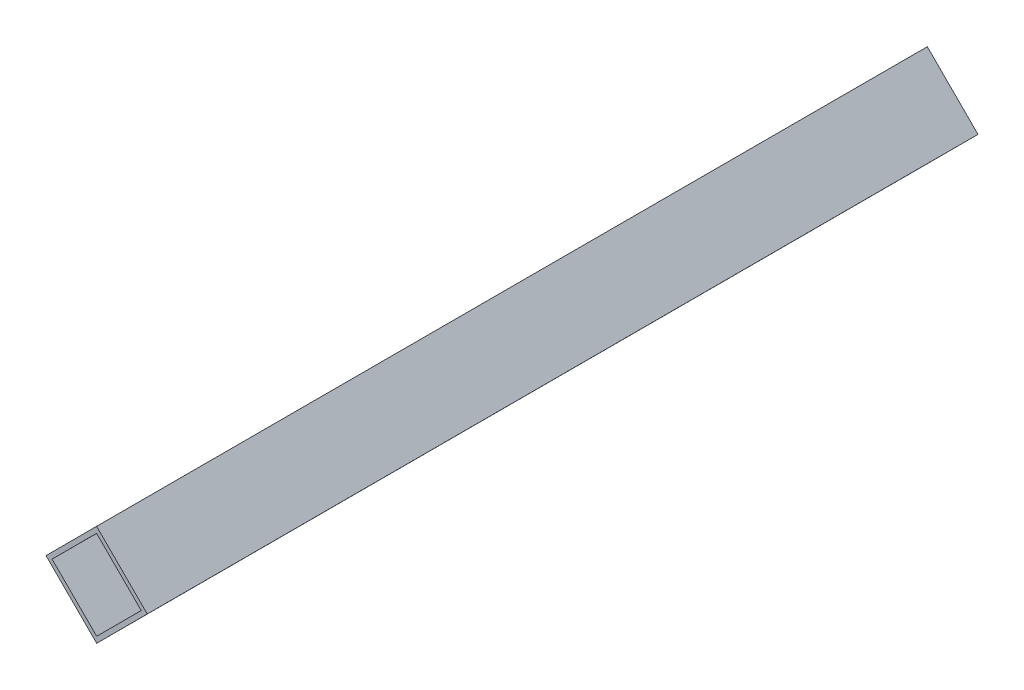
SolidWorks part; units mm, degrees
material "可鍛鑄鐵"
ref_plane "前基準面" through (0, 0, 0) normal (0, 0, 1) x (1, 0, 0)
ref_plane "上基準面" through (0, 0, 0) normal (0, 1, 0) x (1, 0, 0)
ref_plane "右基準面" through (0, 0, 0) normal (1, 0, 0) x (0, 0, -1)
sketch "草圖1" plane through (0, 0, 0) normal (0, 0, 1) x (1, 0, 0)
  line L0 (0, 0) -> (17.6938, -17.6615)
  line L1 (0, 0) -> (-17.6615, -17.6938)
  line L2 (17.6938, -17.6615) -> (0.0323, -35.3553)
  line L3 (-17.6615, -17.6938) -> (0.0323, -35.3553)
  line L4 (0.0019, -2.1213) -> (-15.5402, -17.6919)
  line L5 (0.0019, -2.1213) -> (15.5725, -17.6635)
  line L6 (-15.5402, -17.6919) -> (0.0303, -33.234)
  line L7 (15.5725, -17.6635) -> (0.0303, -33.234)
  point P0 (8.8469, -8.8308)
  dimension "D1" = 25
  dimension "D2" = 25
  dimension "D3" = 1.5
  dimension "D4" = 1.5
  dimension "D5" = 1.5
  dimension "D6" = 1.5
extrude "填料-伸長1" add sketch "草圖1" along normal blind 290
sketch "草圖2" plane through (0, 0, 0) normal (0.7065, 0.7078, 0) x (0.7078, -0.7065, 0)
  line L0 (25, -290) -> (0, -290) construction
  line L1 (25, -290) -> (25, 0) construction
  line L2 (25, 0) -> (0, 0) construction
  line L3 (0, -290) -> (0, 0) construction
  circle A0 centre (12.5, -143) radius 2.75
  circle A1 centre (12.5, -187) radius 2.75
  circle A2 centre (12.5, -103) radius 2.75
  circle A3 centre (12.5, -147) radius 2.75
  dimension "D1" = 5.5
  dimension "D2" = 5.5
  dimension "D4" = 103
  dimension "D5" = 12.5
  dimension "D6" = 12.5
  dimension "D7" = 5.5
  dimension "D8" = 5.5
  dimension "D9" = 44
  dimension "D10" = 103
  dimension "D11" = 12.5
  dimension "D3" = 44
